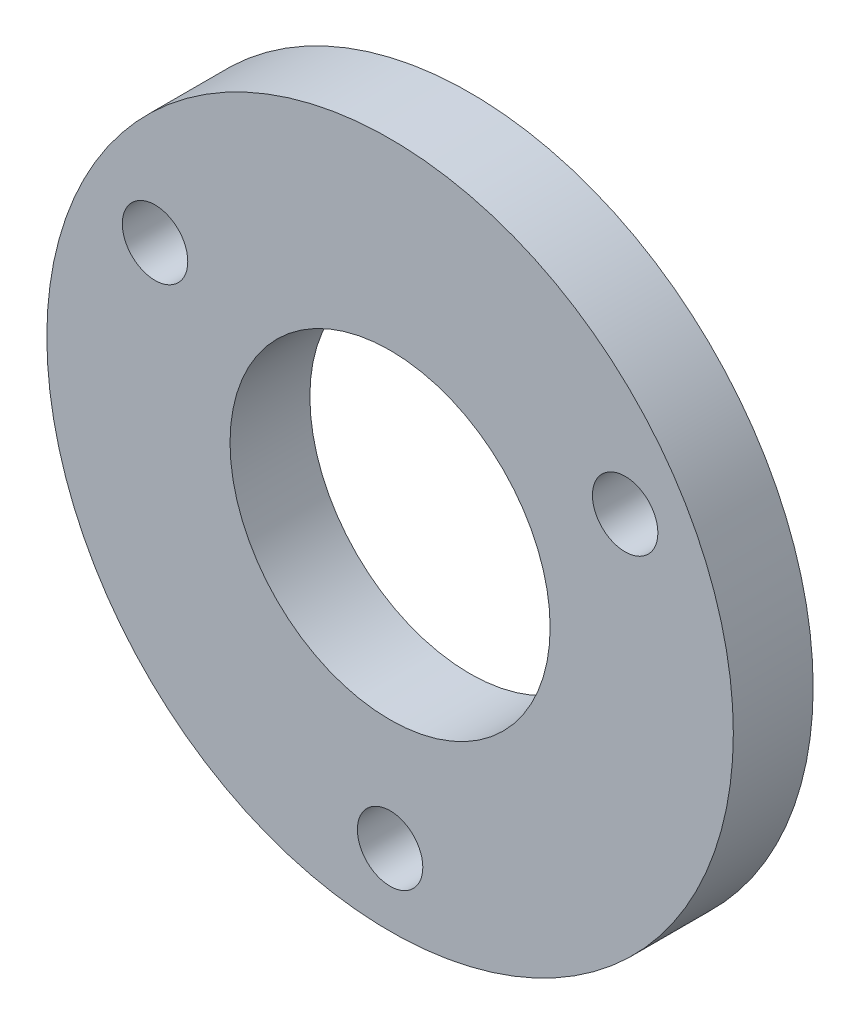
SolidWorks part; units mm, degrees
material "ABS"
ref_plane "正面" through (0, 0, 0) normal (0, 0, 1) x (1, 0, 0)
ref_plane "平面" through (0, 0, 0) normal (0, 1, 0) x (1, 0, 0)
ref_plane "右側面" through (0, 0, 0) normal (1, 0, 0) x (0, 0, -1)
sketch "ｽｹｯﾁ1" plane through (0, 0, 0) normal (0, 0, 1) x (1, 0, 0)
  circle A0 centre (0, 0) radius 21.5
  circle A1 centre (0, 0) radius 18
  dimension "D1" = 43
  dimension "D2" = 36
extrude "ﾎﾞｽ - 押し出し1" add sketch "ｽｹｯﾁ1" along normal blind 5 contours A1 | A0 A1
sketch "ｽｹｯﾁ2" plane through (0, 0, 5) normal (0, 0, 1) x (1, 0, 0)
  circle A0 centre (0, 0) radius 10.025
  dimension "D1" = 20.05
extrude "ｶｯﾄ - 押し出し1" cut sketch "ｽｹｯﾁ2" against normal through all
sketch "ｽｹｯﾁ3" plane through (0, 0, 5) normal (0, 0, 1) x (1, 0, 0)
  circle A0 centre (0, 0) radius 17 construction
  circle A1 centre (0, -17) radius 2.05
  circle A2 centre (-14.7224, 8.5) radius 2.05
  circle A3 centre (14.7224, 8.5) radius 2.05
  point P10 (0, 0)
  dimension "D1" = 34
  dimension "D2" = 4.1
  dimension "D3" = 3
extrude "ｶｯﾄ - 押し出し2" cut sketch "ｽｹｯﾁ3" against normal through all
